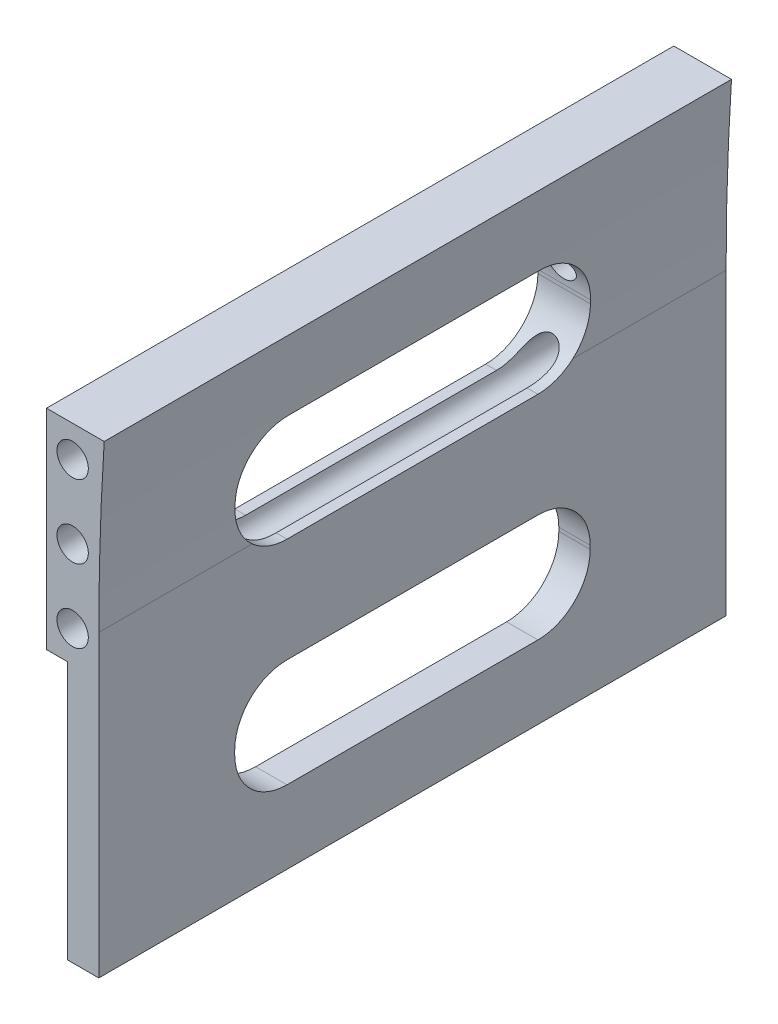
SolidWorks part; units mm, degrees
material "ABS"
ref_plane "Plano frontal" through (0, 0, 0) normal (0, 0, 1) x (1, 0, 0)
ref_plane "Plano superior" through (0, 0, 0) normal (0, 1, 0) x (1, 0, 0)
ref_plane "Plano direito" through (0, 0, 0) normal (1, 0, 0) x (0, 0, -1)
sketch "Esboço1" plane through (0, 0, 0) normal (0, 0, 1) x (1, 0, 0)
  line L0 (13.5691, 56.3389) -> (13.5691, 27.7156)
  line L1 (-13.5691, 56.3389) -> (-13.5691, 27.7156)
  line L2 (-16.3694, 93.6521) -> (-16.5765, 95.0244)
  arc A0 (13.5691, 27.7156) -> (-13.5691, 27.7156) centre (0, 38.1348) cw
  arc A1 (13.5691, 56.3389) -> (14.8299, 81.415) centre (263.5691, 56.3389) cw
  arc A2 (-13.5691, 56.3389) -> (-16.3694, 93.6521) centre (-263.5691, 56.3389) ccw
  arc A3 (14.8299, 81.415) -> (-16.4879, 94.4373) centre (3.2416, 97.7156) ccw
  dimension "D1" = 70
  dimension "D5" = 250
  dimension "D6" = 250
  dimension "D2" = 40
  dimension "D3" = 70
extrude "Ressalto-extrusão1" add sketch "Esboço1" along normal blind 60
sketch "Esboço4" plane through (0, 0, 60) normal (0, 0, 1) x (1, 0, 0)
  circle A0 centre (-4.6155, 109.78) radius 1.5
  circle A1 centre (5.3845, 109.78) radius 1.5
  circle A2 centre (-4.6155, 60) radius 1.5
  circle A3 centre (5.3845, 60) radius 1.5
  arc A4 (14.8299, 81.415) -> (13.5691, 56.3389) centre (263.5691, 56.3389) ccw construction
  point P11 (13.8845, 68.8928)
  dimension "D1" = 49.78
  dimension "D2" = 49.78
  dimension "D3" = 10
  dimension "D4" = 10
  dimension "D5" = 3
  dimension "D6" = 3
  dimension "D7" = 3
  dimension "D8" = 3
  dimension "D9" = 8.5
  dimension "D12" = 10
sketch "Esboço5" plane through (0, 0, 60) normal (0, 0, 1) x (1, 0, 0)
  line L1 (-9.6324, 105.19) -> (10.1676, 105.19)
  line L2 (-9.6324, 105.19) -> (-9.6324, 64.59)
  line L3 (-9.6324, 64.59) -> (10.1676, 64.59)
  line L4 (10.1676, 105.19) -> (10.1676, 64.59)
sketch "Esboço7" plane through (0, 0, 0) normal (0, 0, -1) x (-1, 0, 0)
  line L0 (-10.1676, 105.19) -> (-10.1676, 64.59) construction
  circle A0 centre (-0.2676, 95.19) radius 2.0767
  circle A1 centre (-5.3845, 109.78) radius 1.5 construction
  dimension "D1" = 14.59
  dimension "D2" = 9.9
extrude "Corte-extrusão5" cut sketch "Esboço7" against normal through all
sketch "Esboço8" plane through (0, 0, 60) normal (0, 0, 1) x (1, 0, 0)
  line L1 (38.5703, 81.415) -> (-45.9585, 81.415)
  line L2 (38.5703, 81.415) -> (38.5703, 119.2215)
  line L3 (38.5703, 119.2215) -> (-45.9585, 119.2215)
  line L4 (-45.9585, 81.415) -> (-45.9585, 119.2215)
extrude "Corte-extrusão6" cut sketch "Esboço8" against normal through all
sketch "Esboço9" plane through (0, 0, 60) normal (0, 0, 1) x (1, 0, 0)
  line L1 (13.5691, 27.7156) -> (-25.8016, 27.7156)
  line L2 (13.5691, 27.7156) -> (13.5691, 18.654)
  line L3 (13.5691, 18.654) -> (-25.8016, 18.654)
  line L4 (-25.8016, 27.7156) -> (-25.8016, 18.654)
extrude "Corte-extrusão7" cut sketch "Esboço9" against normal through all
sketch "Esboço10" plane through (0, 0, 60) normal (0, 0, 1) x (1, 0, 0)
  line L0 (13.5691, 27.7156) -> (-13.5691, 27.7156) construction
  line L1 (8.5691, 27.7156) -> (-23.851, 27.7156)
  line L2 (8.5691, 27.7156) -> (8.5691, 89.7448)
  line L3 (8.5691, 89.7448) -> (-23.851, 89.7448)
  line L4 (-23.851, 27.7156) -> (-23.851, 89.7448)
  line L5 (13.5691, 56.3389) -> (13.5691, 27.7156) construction
  point P8 (13.5691, 42.0272)
  dimension "D1" = 5
extrude "Corte-extrusão8" cut sketch "Esboço10" against normal through all
sketch "Esboço12" plane through (0, 0, 60) normal (0, 0, 1) x (1, 0, 0)
  line L0 (8.5691, 81.415) -> (14.8299, 81.415) construction
  line L1 (19.5239, 72.415) -> (1.8289, 72.415)
  line L2 (19.5239, 72.415) -> (19.5239, 81.415)
  line L3 (19.5239, 81.415) -> (1.8289, 81.415)
  line L4 (1.8289, 72.415) -> (1.8289, 81.415)
  dimension "D1" = 0
  dimension "D2" = 9
extrude "Corte-extrusão10" cut sketch "Esboço12" against normal through all
sketch "Esboço13" plane through (0, 0, 60) normal (0, 0, 1) x (1, 0, 0)
  line L0 (13.5691, 56.3389) -> (13.5691, 27.7156) construction
  line L1 (8.5691, 27.7156) -> (10.5691, 27.7156)
  line L2 (8.5691, 27.7156) -> (8.5691, 52.415)
  line L3 (8.5691, 52.415) -> (10.5691, 52.415)
  line L4 (10.5691, 27.7156) -> (10.5691, 52.415)
  dimension "D1" = 3
  dimension "D2" = 20
extrude "Corte-extrusão11" cut sketch "Esboço13" against normal through all
sketch "Esboço14" plane through (8.5691, 0, 0) normal (-1, 0, 0) x (0, 0, 1)
  line L0 (0, 27.7156) -> (60, 27.7156) construction
  line L1 (42, 55.0656) -> (18, 55.0656)
  line L2 (47, 60.0656) -> (47, 60.415)
  line L3 (42, 65.415) -> (18, 65.415)
  line L4 (13, 60.0656) -> (13, 60.415)
  line L5 (42, 34.7156) -> (18, 34.7156)
  line L6 (47, 39.7156) -> (47, 40.0656)
  line L7 (42, 45.0656) -> (18, 45.0656)
  line L8 (13, 39.7156) -> (13, 40.0656)
  line L9 (60, 72.415) -> (0, 72.415) construction
  line L10 (0, 52.415) -> (0, 72.415) construction
  line L11 (60, 52.415) -> (60, 72.415) construction
  line L12 (60, 27.7156) -> (60, 52.415) construction
  line L13 (0, 27.7156) -> (0, 52.415) construction
  arc A0 (42, 55.0656) -> (47, 60.0656) centre (42, 60.0656) ccw
  arc A1 (47, 60.415) -> (42, 65.415) centre (42, 60.415) ccw
  arc A2 (18, 65.415) -> (13, 60.415) centre (18, 60.415) ccw
  arc A3 (18, 55.0656) -> (13, 60.0656) centre (18, 60.0656) cw
  arc A4 (18, 45.0656) -> (13, 40.0656) centre (18, 40.0656) ccw
  arc A5 (18, 34.7156) -> (13, 39.7156) centre (18, 39.7156) cw
  arc A6 (42, 34.7156) -> (47, 39.7156) centre (42, 39.7156) ccw
  arc A7 (47, 40.0656) -> (42, 45.0656) centre (42, 40.0656) ccw
  dimension "D9" = 5
  dimension "D1" = 7
  dimension "D2" = 7
  dimension "D3" = 10
  dimension "D4" = 13
  dimension "D5" = 13
  dimension "D6" = 13
  dimension "D7" = 13
  dimension "D8" = 10.35
extrude "Corte-extrusão12" cut sketch "Esboço14" against normal through all
sketch "Esboço15" plane through (0, 0, 60) normal (0, 0, 1) x (1, 0, 0)
  line L1 (8.5691, 72.415) -> (14.0866, 72.415) construction
  line L2 (10.5691, 52.415) -> (8.5691, 52.415) construction
  circle A0 centre (11.0691, 69.415) radius 1.5
  circle A1 centre (11.0691, 62.415) radius 1.5
  circle A2 centre (11.0691, 55.415) radius 1.5
  point P10 (9.5691, 52.415)
  dimension "D1" = 3
  dimension "D2" = 3
  dimension "D3" = 3
  dimension "D4" = 3
  dimension "D5" = 3
  dimension "D6" = 7
  dimension "D7" = 7
  dimension "D8" = 2.5
  dimension "D9" = 2.5
extrude "Corte-extrusão13" cut sketch "Esboço15" against normal through all
